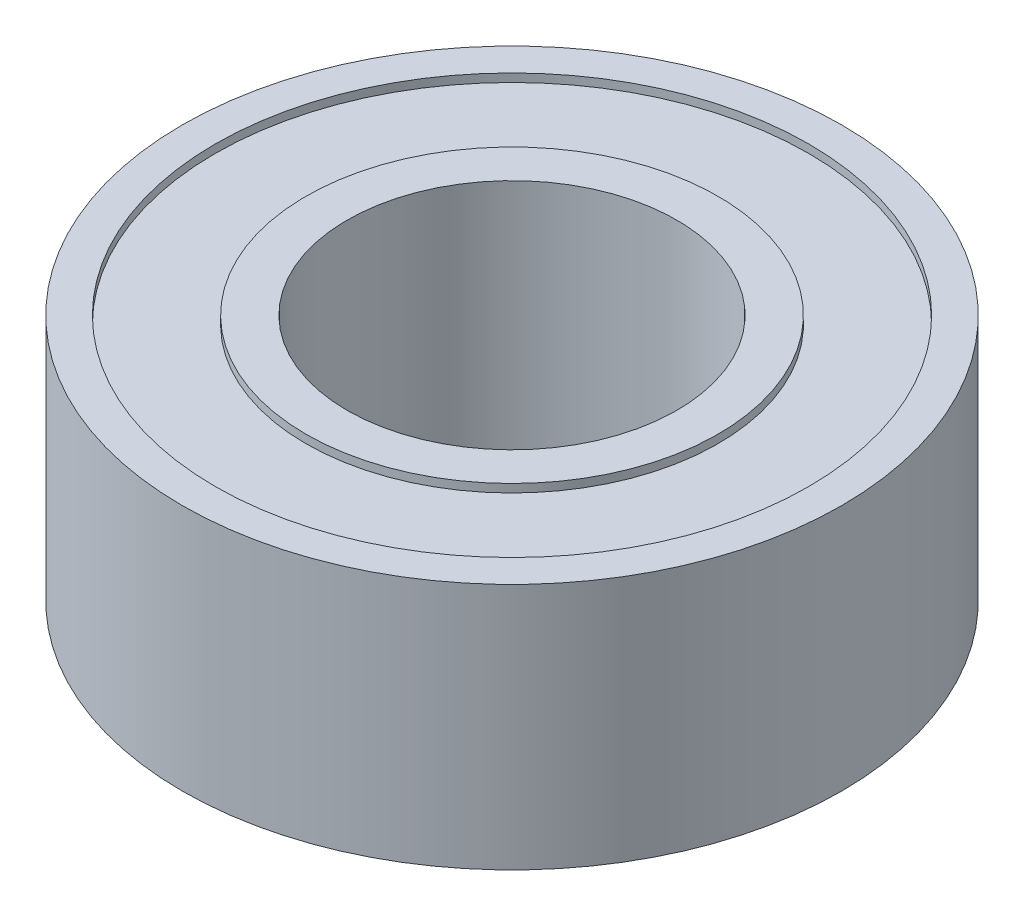
SolidWorks part; units mm, degrees
ref_plane "Спереди" through (0, 0, 0) normal (0, 0, 1) x (1, 0, 0)
ref_plane "Сверху" through (0, 0, 0) normal (0, 1, 0) x (1, 0, 0)
ref_plane "Справа" through (0, 0, 0) normal (1, 0, 0) x (0, 0, -1)
sketch "Эскиз1" plane through (0, 0, 0) normal (0, 1, 0) x (1, 0, 0)
  circle A0 centre (0, 0) radius 4
  circle A1 centre (0, 0) radius 2
extrude "Бобышка-Вытянуть1" add sketch "Эскиз1" along normal blind 3
sketch "Эскиз2" plane through (0, 3, 0) normal (0, 1, 0) x (1, 0, 0)
  circle A0 centre (0, 0) radius 2.5
  circle A1 centre (0, 0) radius 3.6
extrude "Вырез-Вытянуть1" cut sketch "Эскиз2" against normal blind 0.1
sketch "Эскиз3" plane through (0, 0, 0) normal (0, -1, 0) x (1, 0, 0)
  circle A0 centre (0, 0) radius 2.5
  circle A1 centre (0, 0) radius 3.6
extrude "Вырез-Вытянуть2" cut sketch "Эскиз3" against normal blind 0.1
